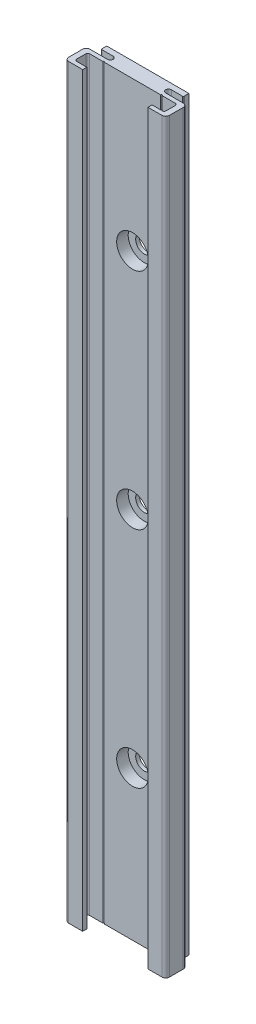
SolidWorks part; units mm, degrees
ref_plane "Front Plane" through (0, 0, 0) normal (0, 0, 1) x (1, 0, 0)
ref_plane "Top Plane" through (0, 0, 0) normal (0, 1, 0) x (1, 0, 0)
ref_plane "Right Plane" through (0, 0, 0) normal (1, 0, 0) x (0, 0, -1)
ref_plane "Plane1" through (0, 300, 0) normal (0, 1, 0) x (1, 0, 0)
sketch "Sketch1" plane through (0, 300, 0) normal (0, 1, 0) x (1, 0, 0)
  line L0 (-13.5, -3) -> (-13.5, -8.7)
  line L1 (-13.5, -8.7) -> (13.5, -8.7)
  line L2 (13.5, -8.7) -> (13.5, -3)
  line L3 (13.5, -3) -> (7.8, -3)
  line L4 (7.8, -1.5) -> (11, -1.5)
  line L5 (11, -1.5) -> (11, 0)
  line L6 (11, 0) -> (-11, 0)
  line L7 (-11, 0) -> (-11, -1.5)
  line L8 (-11, -1.5) -> (-7.8, -1.5)
  line L9 (-7.8, -3) -> (-13.5, -3)
  arc A0 (7.8, -3) -> (7.8, -1.5) centre (7.8, -2.25) cw
  arc A1 (-7.8, -1.5) -> (-7.8, -3) centre (-7.8, -2.25) cw
extrude "Boss-Extrude1" add sketch "Sketch1" against normal blind 200
sketch "Sketch2" plane through (0, 100, 0) normal (0, -1, 0) x (1, 0, 0)
  line L0 (8.75, 8.7) -> (-8.75, 8.7)
  line L1 (-8.75, 8.7) -> (-8.75, 7.6)
  line L2 (-8.75, 7.6) -> (-12, 7.6)
  line L3 (-12, 7.6) -> (-12, 4.1)
  line L4 (-12, 4.1) -> (12, 4.1)
  line L5 (12, 4.1) -> (12, 7.6)
  line L6 (12, 7.6) -> (8.75, 7.6)
  line L7 (8.75, 7.6) -> (8.75, 8.7)
extrude "Cut-Extrude1" cut sketch "Sketch2" against normal through all
hole_wizard "Ø0.4 (0.4) Diameter Hole1" positions "Sketch4" profile "Sketch3" hole size "Ø0.4" standard "ANSI Metric"
sketch "Sketch4" plane through (0, 300, 0) normal (0, 1, 0) x (1, 0, 0)
  point P0 (-7.75, -4.1)
  point P1 (7.75, -4.1)
sketch "Sketch3" plane through (-7.75, 300, 4.1) normal (1, 0, 0) x (0, 0, 1)
  line L0 (0, 0) -> (0, 200)
  line L1 (0, 200) -> (0.2, 200)
  line L2 (0.2, 200) -> (0.2, 0)
  line L5 (0.2, 0) -> (0, 0)
  line L11 (0, -6.35) -> (0, 107.95) construction
  dimension "Thru Hole Dia." = 0.4
  dimension "Thru Hole Depth" = 200
hole_wizard "CBORE for M4 Hex Head Machine Screw1" positions "Sketch6" profile "Sketch5" counterbore size "M4" standard "ANSI Metric"
sketch "Sketch6" plane through (0, 0, 4.1) normal (0, 0, 1) x (1, 0, 0)
  point P0 (0, 260)
  point P1 (0, 200)
  point P2 (0, 140)
  point P3 (0, 80)
  point P4 (0, 20)
sketch "Sketch5" plane through (0, 260, 4.1) normal (1, 0, 0) x (0, -1, 0)
  line L0 (0, 0) -> (0, 4.1)
  line L1 (0, 4.1) -> (2.25, 4.1)
  line L3 (2.25, 4.1) -> (2.25, 3.1)
  line L4 (2.25, 3.1) -> (4.25, 3.1)
  line L5 (4.25, 3.1) -> (4.25, 0)
  line L7 (4.25, 0) -> (0, 0)
  line L11 (0, -6.35) -> (0, 107.95) construction
  dimension "Thru Hole Dia." = 4.5
  dimension "Thru Hole Depth" = 4.1
  dimension "C'Bore Dia." = 8.5
  dimension "C'Bore Depth" = 3.1
fillet "Fillet1" radius 0.2 2 edges at (11, 200, 1.5) (-11, 200, 1.5)
fillet "Fillet2" radius 0.5 4 edges at (12, 200, 4.1) (-12, 200, 7.6) (12, 200, 7.6) (-12, 200, 4.1)
fillet "Fillet3" radius 1 4 edges at (-13.5, 200, 8.7) (-13.5, 200, 3) (13.5, 200, 3) (13.5, 200, 8.7)
